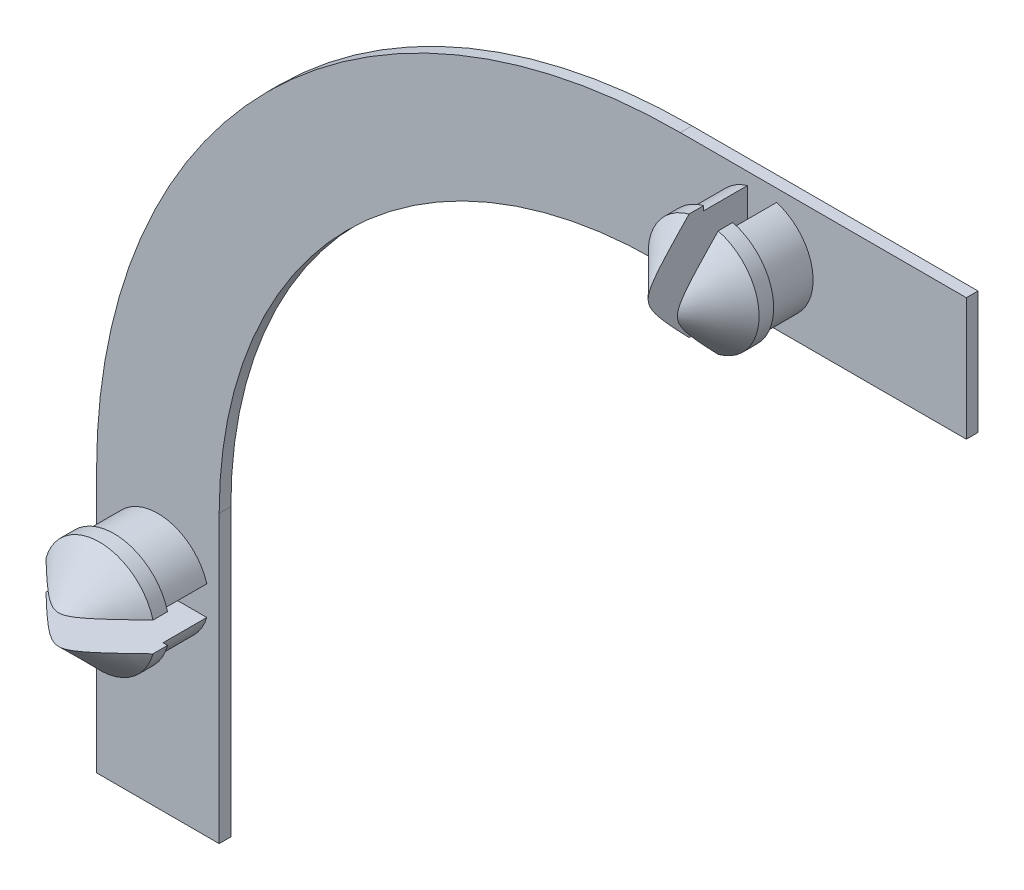
SolidWorks part; units mm, degrees
ref_plane "Přední rovina" through (0, 0, 0) normal (0, 0, 1) x (1, 0, 0)
ref_plane "Horní rovina" through (0, 0, 0) normal (0, 1, 0) x (1, 0, 0)
ref_plane "Pravá rovina" through (0, 0, 0) normal (1, 0, 0) x (0, 0, -1)
sketch "Skica2" plane through (0, 0, 0) normal (0, 0, 1) x (1, 0, 0)
  line L1 (-14.9, 2.1) -> (14.9, 2.1)
  line L2 (-14.9, 2.1) -> (-14.9, -2.1)
  line L3 (-14.9, -2.1) -> (14.9, -2.1)
  line L4 (14.9, 2.1) -> (14.9, -2.1)
  line L5 (-14.9, 2.1) -> (14.9, -2.1) construction
  line L6 (-14.9, -2.1) -> (14.9, 2.1) construction
  point P0 (0, 0)
  point P5 (-1, -0.2)
  dimension "D1" = 4.2
  dimension "D2" = 29.8
extrude "Přidat vysunutím2" add sketch "Skica2" along normal blind 0.4
sketch "Skica3" plane through (0, 0, 0.4) normal (0, 0, 1) x (1, 0, 0)
  line L1 (14.9, -2.1) -> (14.9, 2.1) construction
  circle A1 centre (7.9, 0) radius 1.75
  dimension "D3" = 3.5
  dimension "D4" = 7
extrude "Přidat vysunutím3" add sketch "Skica3" along normal blind 1.5
sketch "Skica5" plane through (0, 0, 1.9) normal (0, 0, 1) x (1, 0, 0)
  circle A1 centre (7.9, 0) radius 1.9
  dimension "D2" = 3.8
extrude "Přidat vysunutím5" add sketch "Skica5" along normal blind 2
chamfer "Zkosení2" distance 1.5 angle 45 1 edges at (9.8, 0, 3.9)
sketch "Skica7" plane through (0, 0, 3.9) normal (0, 0, 1) x (1, 0, 0)
  line L7 (7.4, 2.5) -> (8.4, 2.5)
  line L8 (7.4, 2.5) -> (7.4, -2.5)
  line L9 (7.4, -2.5) -> (8.4, -2.5)
  line L10 (8.4, 2.5) -> (8.4, -2.5)
  line L11 (7.4, 2.5) -> (8.4, -2.5) construction
  line L12 (7.4, -2.5) -> (8.4, 2.5) construction
  point P5 (7.9, 0)
  dimension "D3" = 5
  dimension "D4" = 1
extrude "Odebrat vysunutím1" cut sketch "Skica7" against normal blind 3.5
sketch "Skica8" plane through (0, 0, 0) normal (0, 0, -1) x (-1, 0, 0)
  line L8 (14.9, -2.1) -> (10.7, -2.1)
  line L9 (14.9, -2.1) -> (14.9, -26.9)
  line L10 (14.9, -26.9) -> (10.7, -26.9)
  line L11 (10.7, -2.1) -> (10.7, -26.9)
  dimension "D1" = 24.8
  dimension "D2" = 4.2
extrude "Přidat vysunutím6" add sketch "Skica8" against normal blind 0.4
sketch "Skica9" plane through (0, 0, 0.4) normal (0, 0, 1) x (1, 0, 0)
  line L0 (-10.7, -26.9) -> (-14.9, -26.9) construction
  line L2 (-14.9, 2.1) -> (-14.9, -26.9) construction
  circle A0 centre (-12.8, -19.9) radius 1.75
  dimension "D1" = 3.5
  dimension "D2" = 2.1
  dimension "D3" = 7
extrude "Přidat vysunutím7" add sketch "Skica9" along normal blind 1.5
sketch "Skica10" plane through (0, 0, 1.9) normal (0, 0, 1) x (1, 0, 0)
  circle A0 centre (-12.8, -19.9) radius 1.9
  circle A1 centre (-12.8, -19.9) radius 1.75 construction
  dimension "D1" = 3.8
  dimension "D3" = 0
extrude "Přidat vysunutím8" add sketch "Skica10" along normal blind 2
chamfer "Zkosení3" distance 1.5 angle 45 1 edges at (-10.9, -19.9, 3.9)
sketch "Skica12" plane through (0, 0, 3.9) normal (0, 0, 1) x (1, 0, 0)
  line L1 (-15.3, -19.4) -> (-10.3, -19.4)
  line L2 (-15.3, -19.4) -> (-15.3, -20.4)
  line L3 (-15.3, -20.4) -> (-10.3, -20.4)
  line L4 (-10.3, -19.4) -> (-10.3, -20.4)
  line L5 (-15.3, -19.4) -> (-10.3, -20.4) construction
  line L6 (-15.3, -20.4) -> (-10.3, -19.4) construction
  point P0 (-12.8, -19.9)
  dimension "D1" = 1
  dimension "D2" = 5
extrude "Odebrat vysunutím2" cut sketch "Skica12" against normal blind 3.5
fillet "Zaoblit1" radius 15 1 edges at (-10.7, -2.1, 0.2)
fillet "Zaoblit2" radius 20 1 edges at (-14.9, 2.1, 0.2)
equation "\"1.5.000mm\"=10"
